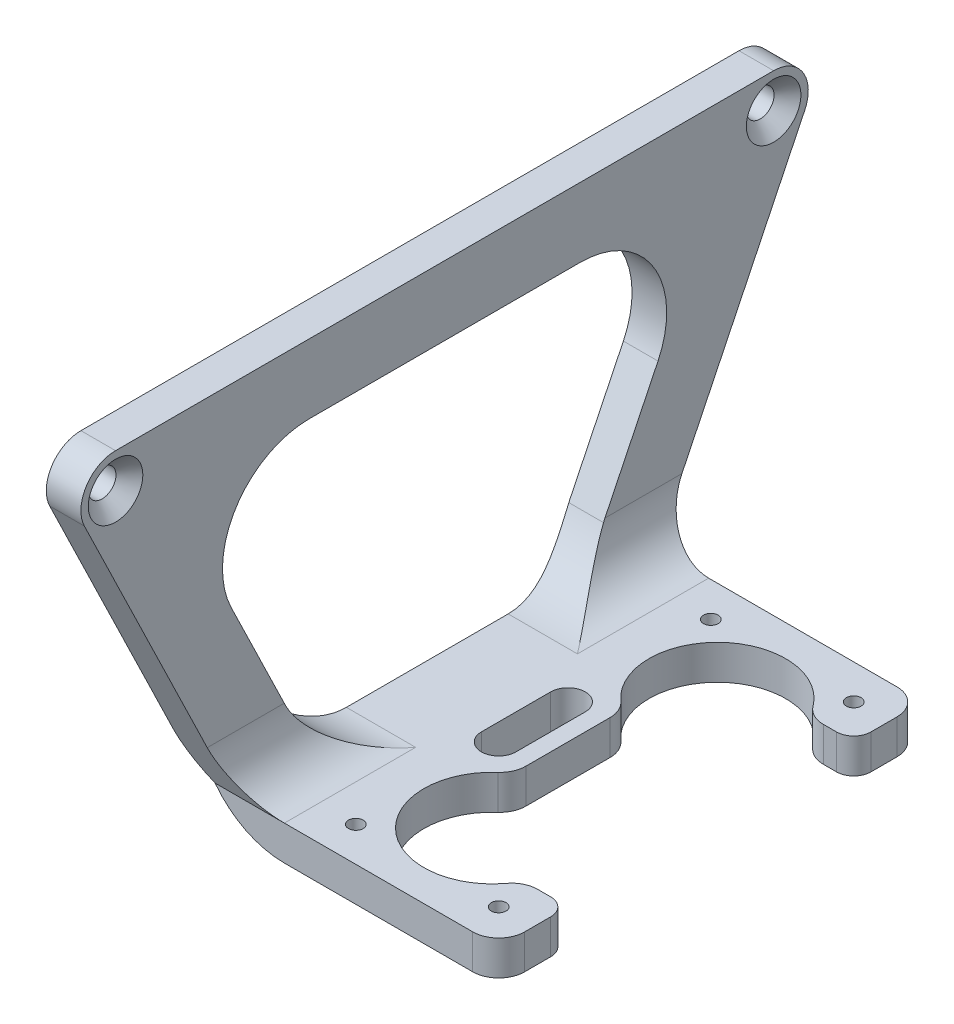
SolidWorks part; units mm, degrees
material "ABS"
ref_plane "Plan de face" through (0, 0, 0) normal (0, 0, 1) x (1, 0, 0)
ref_plane "Plan de dessus" through (0, 0, 0) normal (0, 1, 0) x (1, 0, 0)
ref_plane "Plan de droite" through (0, 0, 0) normal (1, 0, 0) x (0, 0, -1)
sketch "Esquisse1" plane through (0, 0, 0) normal (0, 0, 1) x (1, 0, 0)
  line L0 (0, 0) -> (-25, 0)
  line L1 (-35, 10) -> (-35, 45)
  line L2 (0, 4) -> (-25, 4)
  line L3 (-31, 10) -> (-31, 45)
  line L4 (0, 0) -> (0, 4)
  line L5 (-35, 45) -> (-31, 45)
  arc A2 (-25, 0) -> (-35, 10) centre (-25, 10) cw
  arc A3 (-25, 4) -> (-31, 10) centre (-25, 10) cw
  dimension "D1" = 10
  dimension "D3" = 45
  dimension "D4" = 25
  dimension "D2" = 4
extrude "Boss.-Extru.1" add sketch "Esquisse1" along normal blind 84
hole_wizard "Fraisage pour vis à tête fraisée M31" positions "Esquisse2" profile "Esquisse3" countersink size "M3" standard "ISO" end condition up to next
sketch "Esquisse2" plane through (-31, 0, 0) normal (-1, 0, 0) x (0, 0, 1)
  line L0 (0, 45) -> (0, 10) construction
  line L1 (84, 45) -> (0, 45) construction
  point P0 (4, 41)
  point P2 (80, 41)
  dimension "D1" = 76
  dimension "D2" = 4
  dimension "D3" = 4
sketch "Esquisse3" plane through (-31, 41, 4) normal (0, 1, 0) x (0, 0, -1)
  line L0 (0, 0) -> (0, 4)
  line L1 (0, 4) -> (1.6, 4)
  line L2 (1.6, 4) -> (1.6, 1.55)
  line L3 (1.6, 1.55) -> (3.15, 0)
  line L5 (3.15, 0) -> (0, 0)
  line L6 (-1.6, 1.55) -> (-3.15, 0) construction
  line L11 (0, -6.35) -> (0, 107.95) construction
  dimension "Diamètre du perçage jusqu'au prochain" = 3.2
  dimension "Profondeur du perçage jusqu'au prochain" = 4
  dimension "Diamètre du fraisage entrant" = 6.3
  dimension "Angle du fraisage entrant" = 90
hole_wizard "Dégagement M1.61" positions "Esquisse4" profile "Esquisse5" hole size "M1.6" standard "ISO" end condition up to next
sketch "Esquisse4" plane through (0, 0, 0) normal (0, -1, 0) x (-1, 0, 0)
  line L1 (20.75, -21.5) -> (4.25, -21.5)
  line L2 (20.75, -21.5) -> (20.75, -62.5)
  line L3 (20.75, -62.5) -> (4.25, -62.5)
  line L4 (4.25, -21.5) -> (4.25, -62.5)
  line L5 (20.75, -21.5) -> (4.25, -62.5) construction
  line L6 (20.75, -62.5) -> (4.25, -21.5) construction
  line L7 (25, 0) -> (0, -84) construction
  point P0 (20.75, -21.5)
  point P2 (20.75, -62.5)
  point P4 (4.25, -62.5)
  point P6 (4.25, -21.5)
  point P60 (12.5, -42)
  point P61 (12.5, -42)
  dimension "D1" = 41
  dimension "D2" = 16.5
sketch "Esquisse5" plane through (-20.75, 0, 21.5) normal (1, 0, 0) x (0, 0, -1)
  line L0 (0, 0) -> (0, 4)
  line L1 (0, 4) -> (0.85, 4)
  line L2 (0.85, 4) -> (0.85, 0)
  line L5 (0.85, 0) -> (0, 0)
  line L11 (0, -6.35) -> (0, 107.95) construction
  dimension "Diamètre du perçage jusqu'au prochain" = 1.7
  dimension "Profondeur du perçage jusqu'au prochain" = 4
sketch "Esquisse6" plane through (0, 0, 0) normal (0, -1, 0) x (1, 0, 0)
  line L1 (-35, 17.5) -> (-3.25, 17.5)
  line L2 (-0.25, 20.5) -> (-0.25, 23.5)
  line L3 (-3.25, 66.5) -> (-35, 66.5)
  line L5 (-35, 0) -> (0, 0)
  line L6 (0, 0) -> (0, 84)
  line L7 (0, 84) -> (-35, 84)
  line L8 (-0.25, 60.5) -> (-0.25, 63.5)
  line L9 (-3.7501, 25.5) -> (-2.25, 25.5)
  line L10 (-16.75, 37.1393) -> (-16.75, 46.8607)
  line L11 (-3.7501, 58.5) -> (-2.25, 58.5)
  line L13 (-19.25, 42) -> (0, 42) construction
  line L14 (-4.25, 62.5) -> (-12.5, 55) construction
  line L15 (-12.5, 55) -> (-20.75, 62.5) construction
  line L17 (0, 84) -> (0, 0) construction
  line L18 (-35, 84) -> (-35, 0) construction
  line L19 (-35, 66.5) -> (-35, 84)
  line L20 (-35, 17.5) -> (-35, 0)
  line L21 (-20.75, 46) -> (-20.75, 38) construction
  line L22 (-18.75, 46) -> (-18.75, 38)
  line L23 (-22.75, 46) -> (-22.75, 38)
  circle A0 centre (-4.25, 21.5) radius 0.85 construction
  circle A1 centre (-4.25, 62.5) radius 0.85 construction
  arc A2 (-0.25, 63.5) -> (-3.25, 66.5) centre (-3.25, 63.5) ccw
  arc A3 (-3.25, 17.5) -> (-0.25, 20.5) centre (-3.25, 20.5) ccw
  circle A6 centre (-20.75, 21.5) radius 0.85 construction
  circle A7 centre (-20.75, 62.5) radius 0.85 construction
  arc A12 (-6.1584, 59.711) -> (-17.7546, 49.1009) centre (-12.5, 55) ccw
  arc A13 (-17.7546, 34.8991) -> (-6.1584, 24.289) centre (-12.5, 29) ccw
  arc A14 (-6.1584, 24.289) -> (-3.7501, 25.5) centre (-3.7501, 22.5) cw
  arc A15 (-17.7546, 34.8991) -> (-16.75, 37.1393) centre (-19.75, 37.1393) ccw
  arc A16 (-3.7501, 58.5) -> (-6.1584, 59.711) centre (-3.7501, 61.5) cw
  arc A17 (-16.75, 46.8607) -> (-17.7546, 49.1009) centre (-19.75, 46.8607) ccw
  arc A18 (-2.25, 25.5) -> (-0.25, 23.5) centre (-2.25, 23.5) cw
  arc A19 (-2.25, 58.5) -> (-0.25, 60.5) centre (-2.25, 60.5) ccw
  arc A20 (-18.75, 46) -> (-22.75, 46) centre (-20.75, 46) ccw
  arc A21 (-22.75, 38) -> (-18.75, 38) centre (-20.75, 38) ccw
  point P8 (-20.75, 42)
  point P40 (-0.25, 58.5)
  point P48 (0, 0)
  dimension "D1" = 4
  dimension "D2" = 4
  dimension "D5" = 4
  dimension "D6" = 3
  dimension "D7" = 8
  dimension "D12" = 3
  dimension "D11" = 15.8
  dimension "D3" = 2
  dimension "D4" = 4
  dimension "D8" = 4
  dimension "D9" = 4
  dimension "D10" = 4
  dimension "D13" = 26
  dimension "D14" = 4
extrude "Enlèv. mat.-Extru.1" cut sketch "Esquisse6" against normal up to surface (4 mm away) up to face at (-19.9, 4, 21.5)
sketch "Esquisse7" plane through (-31, 0, 0) normal (1, 0, 0) x (0, 0, -1)
  line L0 (-66.5, 4) -> (-17.5, 4) construction
  line L5 (0, 41) -> (0, 45)
  line L6 (0, 4) -> (0, 41)
  line L7 (-17.5, 4) -> (-0.401, 39.2544)
  line L8 (-66.5, 4) -> (-83.599, 39.2544)
  line L10 (0, 45) -> (-4, 45)
  line L12 (-84, 41) -> (-84, 45)
  line L14 (-84, 41) -> (-84, 4)
  line L16 (-84, 4) -> (-66.5, 4)
  line L17 (-17.5, 4) -> (0, 4)
  line L19 (-26.3501, 37) -> (-57.6499, 37)
  line L20 (-66.6475, 22.636) -> (-60.3423, 9.636)
  line L21 (-51.3447, 4) -> (-32.6553, 4)
  line L22 (-23.6577, 9.636) -> (-17.3525, 22.636)
  line L23 (-84, 45) -> (-80, 45)
  arc A2 (-26.3501, 37) -> (-17.3525, 22.636) centre (-26.3501, 27) cw
  arc A3 (-57.6499, 37) -> (-66.6475, 22.636) centre (-57.6499, 27) ccw
  arc A10 (-60.3423, 9.636) -> (-51.3447, 4) centre (-51.3447, 14) ccw
  arc A11 (-32.6553, 4) -> (-23.6577, 9.636) centre (-32.6553, 14) ccw
  arc A13 (-0.401, 39.2544) -> (-4, 45) centre (-4, 41) ccw
  arc A14 (-80, 45) -> (-83.599, 39.2544) centre (-80, 41) ccw
  line M10 (0, 10) -> (0, 45)
  line M12 (0, 45) -> (-84, 45)
  line M14 (-84, 45) -> (-84, 10)
  line M15 (-84, 10) -> (0, 10)
  dimension "D1" = 10
extrude "Enlèv. mat.-Extru.2" cut sketch "Esquisse7" against normal through all and the other way through all contours L19 A3 L20 L22 A2 M15 | L21 A11 L22 L20 A10 M15 | L7 L17 L6 M15 | A13 L7 M15 M10 | A13 M10 M12 | A14 L8 M14 M15 | L14 L16 L8 M15 | A14 M12 M14
